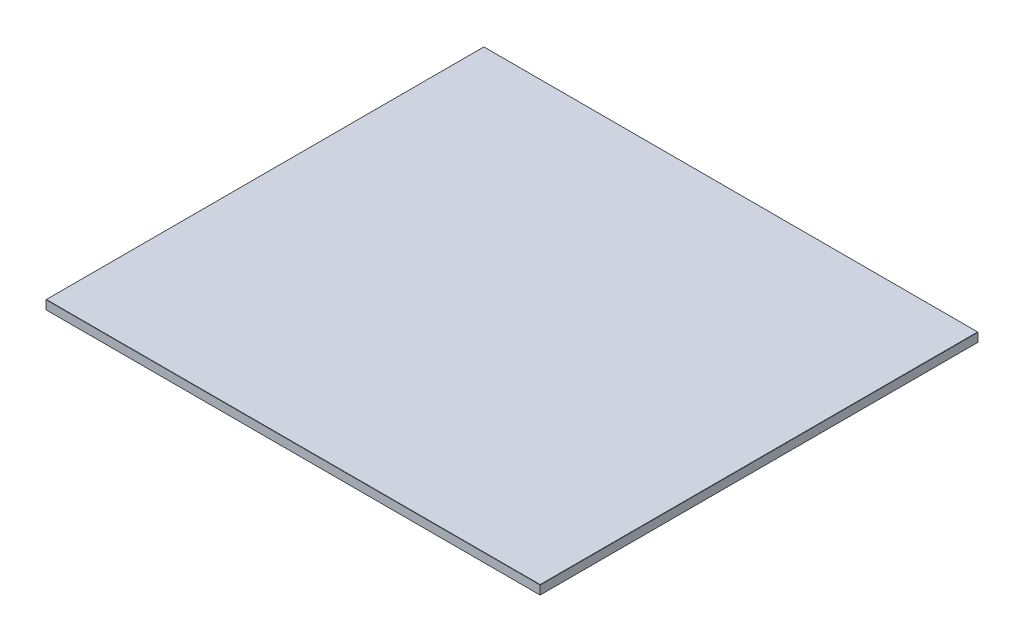
SolidWorks part; units mm, degrees
ref_plane "Front Plane" through (0, 0, 0) normal (0, 0, 1) x (1, 0, 0)
ref_plane "Top Plane" through (0, 0, 0) normal (0, 1, 0) x (1, 0, 0)
ref_plane "Right Plane" through (0, 0, 0) normal (1, 0, 0) x (0, 0, -1)
sketch "Sketch1" plane through (0, 0, 0) normal (0, 1, 0) x (1, 0, 0)
  line L1 (-325, -288) -> (325, -288)
  line L2 (-325, -288) -> (-325, 288)
  line L3 (-325, 288) -> (325, 288)
  line L4 (325, -288) -> (325, 288)
  line L5 (-325, -288) -> (325, 288) construction
  line L6 (-325, 288) -> (325, -288) construction
  point P0 (0, 0)
  dimension "D1" = 576
  dimension "D2" = 650
extrude "Boss-Extrude1" add sketch "Sketch1" along normal blind 12
chamfer "Chamfer1" distance 0.25 angle 45 8 edges at (0, 0, -288) (-325, 0, 0) (0, 0, 288) (325, 0, 0) (0, 12, 288) (-325, 12, 0) (0, 12, -288) (325, 12, 0)
